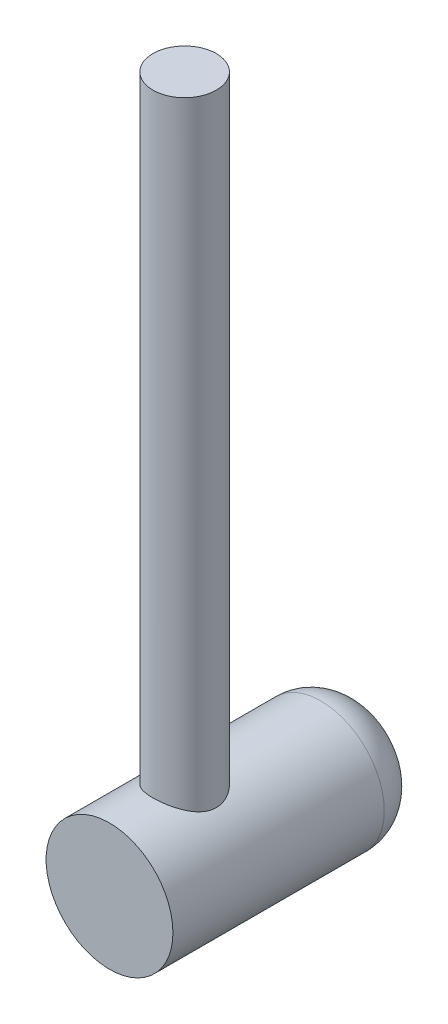
SolidWorks part; units mm, degrees
ref_plane "Front Plane" through (0, 0, 0) normal (0, 0, 1) x (1, 0, 0)
ref_plane "Top Plane" through (0, 0, 0) normal (0, 1, 0) x (1, 0, 0)
ref_plane "Right Plane" through (0, 0, 0) normal (1, 0, 0) x (0, 0, -1)
sketch "Sketch1" plane through (0, 0, 0) normal (0, 0, 1) x (1, 0, 0)
  circle A0 centre (0, 0) radius 750
  dimension "D1" = 1500
extrude "Boss-Extrude1" add sketch "Sketch1" along normal blind 3000
fillet "Fillet1" radius 500 1 edges at (750, 0, 0)
sketch "Sketch2" plane through (0, 0, 0) normal (0, 1, 0) x (1, 0, 0)
  circle A0 centre (0, -2111.6355) radius 375
  point P2 (0, -2111.6355)
  dimension "D1" = 750
extrude "Boss-Extrude2" add sketch "Sketch2" along normal blind 8000
